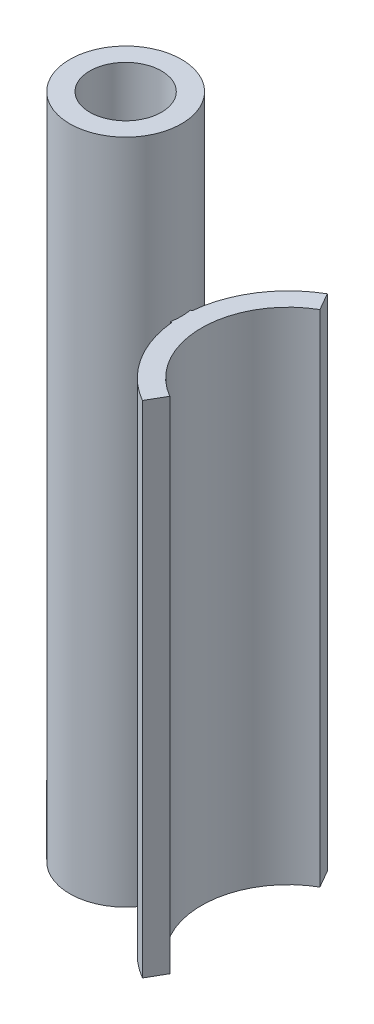
SolidWorks part; units mm, degrees
ref_plane "Front Plane" through (0, 0, 0) normal (0, 0, 1) x (1, 0, 0)
ref_plane "Top Plane" through (0, 0, 0) normal (0, 1, 0) x (1, 0, 0)
ref_plane "Right Plane" through (0, 0, 0) normal (1, 0, 0) x (0, 0, -1)
sketch "Sketch1" plane through (0, 0, 0) normal (0, 1, 0) x (1, 0, 0)
  circle A0 centre (0, 0) radius 5.375
  circle A1 centre (0, 0) radius 8.375
  dimension "D1" = 3
  dimension "D2" = 10.75
extrude "Boss-Extrude1" add sketch "Sketch1" along normal blind 100
sketch "Sketch2" plane through (0, 0, 0) normal (0, 1, 0) x (1, 0, 0)
  line L0 (5.375, 0) -> (11.375, 0)
  line L1 (11.4618, 1.5) -> (8.2396, 1.5)
  line L2 (0, 0) -> (5.375, 0) construction
  line L3 (11.4618, -1.5) -> (8.2396, -1.5)
  line L4 (24.375, 0) -> (11.375, 0) construction
  line L5 (24.375, 0) -> (16.375, 13.8564)
  line L6 (24.375, 0) -> (16.375, -13.8564)
  circle A0 centre (24.375, 0) radius 16
  circle A1 centre (0, 0) radius 8.375
  circle A2 centre (24.375, 0) radius 13
  circle A3 centre (0, 0) radius 5.375 construction
  circle A4 centre (0, 0) radius 8.375 construction
  dimension "D1" = 26
  dimension "D5" = 3
  dimension "D2" = 6
  dimension "D3" = 1.5
  dimension "D6" = 60
extrude "Boss-Extrude2" add sketch "Sketch2" along normal blind 75 contours A1 L0 A0 L1 | A1 L3 A0 L0 | A2 L1 A0 L0 | A2 L0 A0 L3 | A2 L5 A0 L1 | A2 L3 A0 L6
